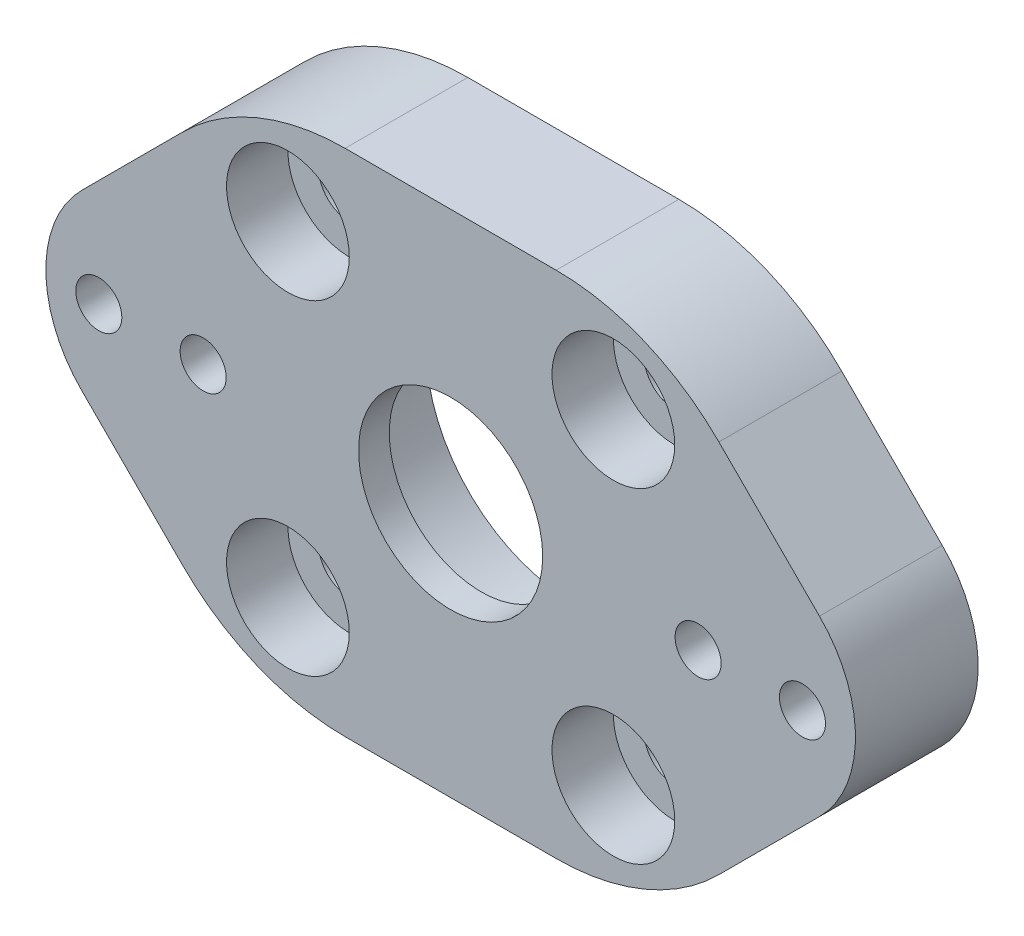
SolidWorks part; units mm, degrees
material "ABS PC"
ref_plane "Front Plane" through (0, 0, 0) normal (0, 0, 1) x (1, 0, 0)
ref_plane "Top Plane" through (0, 0, 0) normal (0, 1, 0) x (1, 0, 0)
ref_plane "Right Plane" through (0, 0, 0) normal (1, 0, 0) x (0, 0, -1)
sketch "Sketch1" plane through (0, 0, 0) normal (0, 0, 1) x (1, 0, 0)
  line L0 (15, 0) -> (0, 0) construction
  line L1 (0, 0) -> (10.6066, 10.6066) construction
  line L2 (-29.6985, 0) -> (0, 29.6985)
  line L3 (0, 29.6985) -> (29.6985, 0)
  line L4 (29.6985, 0) -> (0, -29.6985)
  line L5 (0, -29.6985) -> (-29.6985, 0)
  line L6 (-29.6985, 0) -> (0, 0) construction
  line L7 (0, 0) -> (29.6985, 0) construction
  line L8 (0, 29.6985) -> (0, 0) construction
  line L9 (0, 0) -> (0, -29.6985) construction
  circle A0 centre (0, 0) radius 15 construction
  circle A1 centre (10.6066, 10.6066) radius 2
  circle A2 centre (10.6066, -10.6066) radius 2
  circle A3 centre (-10.6066, -10.6066) radius 2
  circle A4 centre (-10.6066, 10.6066) radius 2
  circle A5 centre (0, 0) radius 9.6
  point P15 (0, 0)
  dimension "D1" = 30
  dimension "D2" = 4
  dimension "D5" = 19.2
  dimension "D6" = 42
  dimension "D3" = 45
  dimension "D4" = 4
extrude "Boss-Extrude1" add sketch "Sketch1" along normal blind 8
sketch "Sketch2" plane through (0, 0, 8) normal (0, 0, 1) x (1, 0, 0)
  circle A0 centre (-10.6066, 10.6066) radius 4
  circle A1 centre (10.6066, 10.6066) radius 4
  circle A2 centre (10.6066, -10.6066) radius 4
  circle A3 centre (-10.6066, -10.6066) radius 4
  point P12 (0, 0)
  dimension "D1" = 8
  dimension "D2" = 4
extrude "Cut-Extrude1" cut sketch "Sketch2" against normal blind 4
sketch "Sketch3" plane through (0, 0, 8) normal (0, 0, 1) x (1, 0, 0)
  line L0 (-22.9312, -0.2137) -> (-16.1312, -0.2137) construction
  line L1 (-16.1312, -0.2137) -> (16.1312, -0.2162) construction
  line L2 (16.1312, -0.2162) -> (22.9312, -0.2162) construction
  circle A0 centre (-22.9312, -0.2137) radius 1.5
  circle A1 centre (-16.1312, -0.2137) radius 1.5
  circle A2 centre (16.1312, -0.2162) radius 1.5
  circle A3 centre (22.9312, -0.2162) radius 1.5
  dimension "D1" = 3
  dimension "D2" = 6.8
  dimension "D3" = 0.215
extrude "Cut-Extrude2" cut sketch "Sketch3" against normal blind 10
sketch "Sketch4" plane through (0, 0, 0) normal (0, 0, -1) x (-1, 0, 0)
  line L1 (-24.4467, 2.4088) -> (-25.9623, -0.2162)
  line L2 (-25.9623, -0.2162) -> (-24.4467, -2.8412)
  line L3 (-24.4467, -2.8412) -> (-21.4157, -2.8412)
  line L4 (-21.4157, -2.8412) -> (-19.9001, -0.2162)
  line L5 (-19.9001, -0.2162) -> (-21.4157, 2.4088)
  line L6 (-21.4157, 2.4088) -> (-24.4467, 2.4088)
  line L7 (-13.5062, 1.2993) -> (-16.1312, 2.8149)
  line L8 (-16.1312, 2.8149) -> (-18.7562, 1.2993)
  line L9 (-18.7562, 1.2993) -> (-18.7562, -1.7318)
  line L10 (-18.7562, -1.7318) -> (-16.1312, -3.2473)
  line L11 (-16.1312, -3.2473) -> (-13.5062, -1.7318)
  line L12 (-13.5062, -1.7318) -> (-13.5062, 1.2993)
  line L13 (18.7562, 1.3018) -> (16.1312, 2.8174)
  line L14 (16.1312, 2.8174) -> (13.5062, 1.3018)
  line L15 (13.5062, 1.3018) -> (13.5062, -1.7293)
  line L16 (13.5062, -1.7293) -> (16.1312, -3.2448)
  line L17 (16.1312, -3.2448) -> (18.7562, -1.7293)
  line L18 (18.7562, -1.7293) -> (18.7562, 1.3018)
  line L19 (21.4157, 2.4113) -> (19.9001, -0.2137)
  line L20 (19.9001, -0.2137) -> (21.4157, -2.8387)
  line L21 (21.4157, -2.8387) -> (24.4467, -2.8387)
  line L22 (24.4467, -2.8387) -> (25.9623, -0.2137)
  line L23 (25.9623, -0.2137) -> (24.4467, 2.4113)
  line L24 (24.4467, 2.4113) -> (21.4157, 2.4113)
  circle A0 centre (-22.9312, -0.2162) radius 2.625 construction
  circle A1 centre (-16.1312, -0.2162) radius 2.625 construction
  circle A2 centre (16.1312, -0.2137) radius 2.625 construction
  circle A3 centre (22.9312, -0.2137) radius 2.625 construction
  circle A4 centre (16.1312, -0.2137) radius 1.5 construction
  circle A5 centre (-22.9312, -0.2162) radius 1.5 construction
  circle A6 centre (-16.1312, -0.2162) radius 1.5 construction
  dimension "D1" = 5.25
extrude "Cut-Extrude3" cut sketch "Sketch4" against normal blind 3
fillet "Fillet1" radius 8 2 edges at (-29.6985, 0, 4) (29.6985, 0, 4)
sketch "Sketch5" plane through (0, 0, 8) normal (0, 0, 1) x (1, 0, 0)
  line L0 (0, 29.6985) -> (-24.0416, 5.6569) construction
  line L1 (0, -29.6985) -> (24.0416, -5.6569) construction
  line L2 (-24.0416, -5.6569) -> (0, -29.6985) construction
  line L3 (24.0416, 5.6569) -> (0, 29.6985) construction
  line L4 (0, -29.6985) -> (13.0919, -16.6066)
  line L5 (-13.0919, -16.6066) -> (0, -29.6985)
  line L6 (0, 29.6985) -> (-13.0919, 16.6066)
  line L7 (13.0919, 16.6066) -> (0, 29.6985)
  line L8 (-13.0919, 16.6066) -> (13.0919, 16.6066)
  line L9 (13.0919, -16.6066) -> (-13.0919, -16.6066)
  line L10 (-24.0416, -5.6569) -> (0, -29.6985)
  circle A6 centre (-10.6066, 10.6066) radius 4 construction
  circle A7 centre (-10.6066, -10.6066) radius 4 construction
  line M10 (0, 29.6985) -> (-24.0416, 5.6569)
  line M12 (-24.0416, -5.6569) -> (0, -29.6985)
  line M13 (0, -29.6985) -> (24.0416, -5.6569)
  line M15 (24.0416, 5.6569) -> (0, 29.6985)
  dimension "D1" = 6
  dimension "D2" = 6
extrude "Cut-Extrude4" cut sketch "Sketch5" against normal through all contours L8 M10 M15 | L9 M13 M12
fillet "Fillet2" radius 15 4 edges at (-13.0919, -16.6066, 4) (13.0919, -16.6066, 4) (13.0919, 16.6066, 4) (-13.0919, 16.6066, 4)
fillet "Fillet3" [suppressed] radius 1
sketch "Sketch7" plane through (0, 0, 8) normal (0, 0, 1) x (1, 0, 0)
  circle A0 centre (0, 0) radius 6
  circle A1 centre (0, 0) radius 9.6
  circle A2 centre (0, 0) radius 9.6 construction
  dimension "D1" = 12
extrude "Boss-Extrude2" add sketch "Sketch7" against normal blind 2
